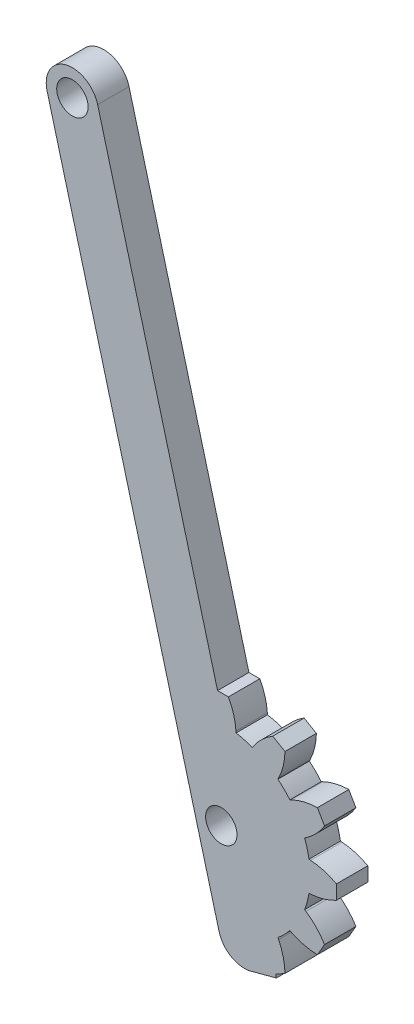
SolidWorks part; units mm, degrees
ref_plane "Front Plane" through (0, 0, 0) normal (0, 0, 1) x (1, 0, 0)
ref_plane "Top Plane" through (0, 0, 0) normal (0, 1, 0) x (1, 0, 0)
ref_plane "Right Plane" through (0, 0, 0) normal (1, 0, 0) x (0, 0, -1)
ref_plane "Plane1" through (0, 0, 1.9) normal (0, 0, 1) x (1, 0, 0)
sketch "Sketch1" plane through (0, 0, 1.9) normal (0, 0, 1) x (1, 0, 0)
  line L0 (-16.6499, 52.4789) -> (-0.2149, -8.8574)
  line L1 (2.847, -10.6252) -> (5.2618, -9.9781)
  line L2 (5.2618, -9.9781) -> (5.1889, -9.7059)
  line L3 (5.1889, -9.7059) -> (6.0876, -9.187)
  line L4 (5.4819, -6.6916) -> (5.4141, -6.5527)
  line L5 (6.5527, -5.4141) -> (6.6916, -5.4819)
  line L6 (9.187, -6.0876) -> (9.8655, -4.9124)
  line L7 (8.0933, -3.0542) -> (7.9651, -2.9677)
  line L8 (8.3818, -1.4124) -> (8.5361, -1.4016)
  line L9 (11, -0.6785) -> (11, 0.6785)
  line L10 (8.5361, 1.4016) -> (8.3818, 1.4124)
  line L11 (7.9651, 2.9677) -> (8.0933, 3.0542)
  line L12 (9.8655, 4.9124) -> (9.187, 6.0876)
  line L13 (6.6916, 5.4819) -> (6.5527, 5.4141)
  line L14 (5.4141, 6.5527) -> (5.4819, 6.6916)
  line L15 (6.0876, 9.187) -> (4.9124, 9.8655)
  line L16 (3.0542, 8.0933) -> (2.9677, 7.9651)
  line L17 (1.4124, 8.3818) -> (1.4016, 8.5361)
  line L18 (0.6785, 11) -> (-0.3593, 11)
  line L19 (-0.3593, 11) -> (-11.8202, 53.773)
  circle A0 centre (-14.235, 53.1259) radius 1.5
  arc A1 (-0.2149, -8.8574) -> (2.847, -10.6252) centre (2.2, -8.2104) ccw
  arc A2 (6.0876, -9.187) -> (5.4819, -6.6916) centre (0.0891, -9.3218) ccw
  arc A3 (5.4141, -6.5527) -> (6.5527, -5.4141) centre (0, 0) ccw
  arc A4 (6.6916, -5.4819) -> (9.187, -6.0876) centre (9.3218, -0.0891) ccw
  arc A5 (9.8655, -4.9124) -> (8.0933, -3.0542) centre (4.7381, -8.0284) ccw
  arc A6 (7.9651, -2.9677) -> (8.3818, -1.4124) centre (0, 0) ccw
  arc A7 (8.5361, -1.4016) -> (11, -0.6785) centre (8.1175, 4.5837) ccw
  arc A8 (11, 0.6785) -> (8.5361, 1.4016) centre (8.1175, -4.5837) ccw
  arc A9 (8.3818, 1.4124) -> (7.9651, 2.9677) centre (0, 0) ccw
  arc A10 (8.0933, 3.0542) -> (9.8655, 4.9124) centre (4.7381, 8.0284) ccw
  arc A11 (9.187, 6.0876) -> (6.6916, 5.4819) centre (9.3218, 0.0891) ccw
  arc A12 (6.5527, 5.4141) -> (5.4141, 6.5527) centre (0, 0) ccw
  arc A13 (5.4819, 6.6916) -> (6.0876, 9.187) centre (0.0891, 9.3218) ccw
  arc A14 (4.9124, 9.8655) -> (3.0542, 8.0933) centre (8.0284, 4.7381) ccw
  arc A15 (2.9677, 7.9651) -> (1.4124, 8.3818) centre (0, 0) ccw
  arc A16 (1.4016, 8.5361) -> (0.6785, 11) centre (-4.5837, 8.1175) ccw
  arc A17 (-11.8202, 53.773) -> (-16.6499, 52.4789) centre (-14.235, 53.1259) ccw
  circle A18 centre (0, 0) radius 1.5
  dimension "D1" = 3
  dimension "D2" = 2.5
  dimension "D3" = 0.0891
  dimension "D4" = 8.5
  dimension "D5" = 6
  dimension "D6" = 0.6785
  dimension "D7" = 1.4016
  dimension "D8" = 1.4124
  dimension "D9" = 2.2
  dimension "D10" = 2.847
  dimension "D11" = 2.9677
  dimension "D12" = 3.0542
  dimension "D13" = 4.7381
  dimension "D14" = 4.9124
  dimension "D15" = 5.1889
  dimension "D16" = 5.4141
  dimension "D17" = 6.5527
  dimension "D18" = 8.1175
  dimension "D19" = 55
extrude "Boss-Extrude1" add sketch "Sketch1" against normal blind 3
